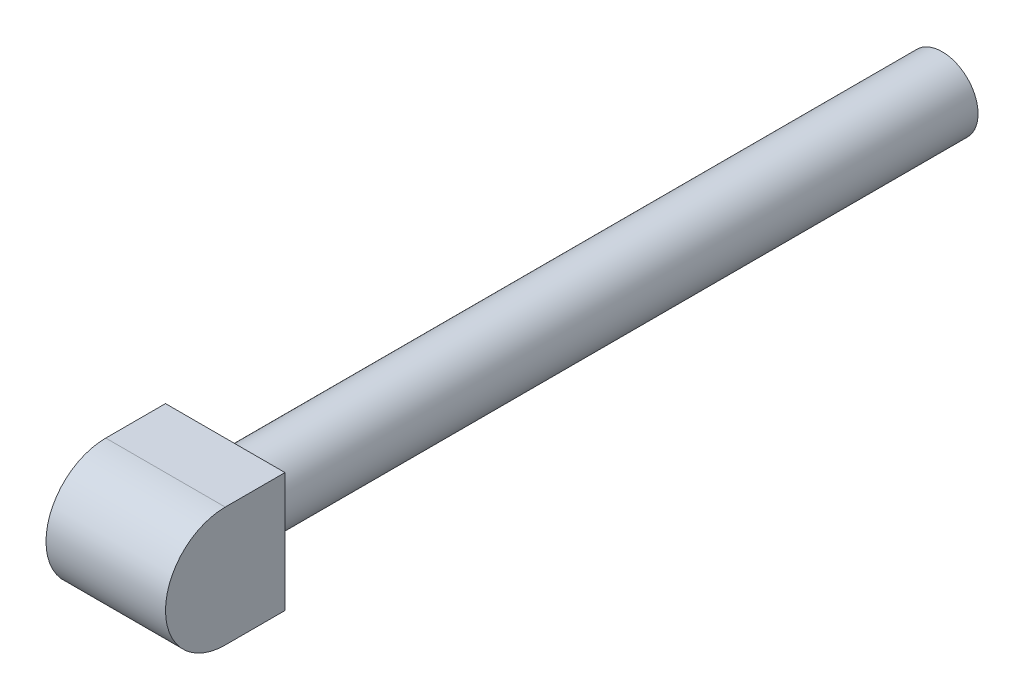
SolidWorks part; units mm, degrees
ref_plane "Front" through (0, 0, 0) normal (0, 0, 1) x (1, 0, 0)
ref_plane "Top" through (0, 0, 0) normal (0, 1, 0) x (1, 0, 0)
ref_plane "Right" through (0, 0, 0) normal (1, 0, 0) x (0, 0, -1)
sketch "草图1" plane through (0, 0, 0) normal (0, 0, 1) x (1, 0, 0)
  line L1 (-10, 10) -> (10, 10)
  line L2 (-10, 10) -> (-10, -10)
  line L3 (-10, -10) -> (10, -10)
  line L4 (10, 10) -> (10, -10)
  dimension "D1" = 20
  dimension "D2" = 20
  dimension "D3" = 10
  dimension "D4" = 10
extrude "凸台-拉伸1" add sketch "草图1" along normal blind 20
sketch "草图2" plane through (0, 0, 0) normal (0, 0, -1) x (-1, 0, 0)
  circle A0 centre (0, 0) radius 6
extrude "凸台-拉伸2" add sketch "草图2" along normal blind 120
sketch "草图3" plane through (10, 0, 0) normal (1, 0, 0) x (0, 0, -1)
  line L1 (-10, 10) -> (-23.0531, 10)
  line L3 (-10, -10) -> (-23.0531, -10)
  line L4 (-23.0531, 10) -> (-23.0531, -10)
  arc A0 (-10, 10) -> (-10, -10) centre (-10, 0) ccw
extrude "切除-拉伸1" cut sketch "草图3" against normal blind 70
